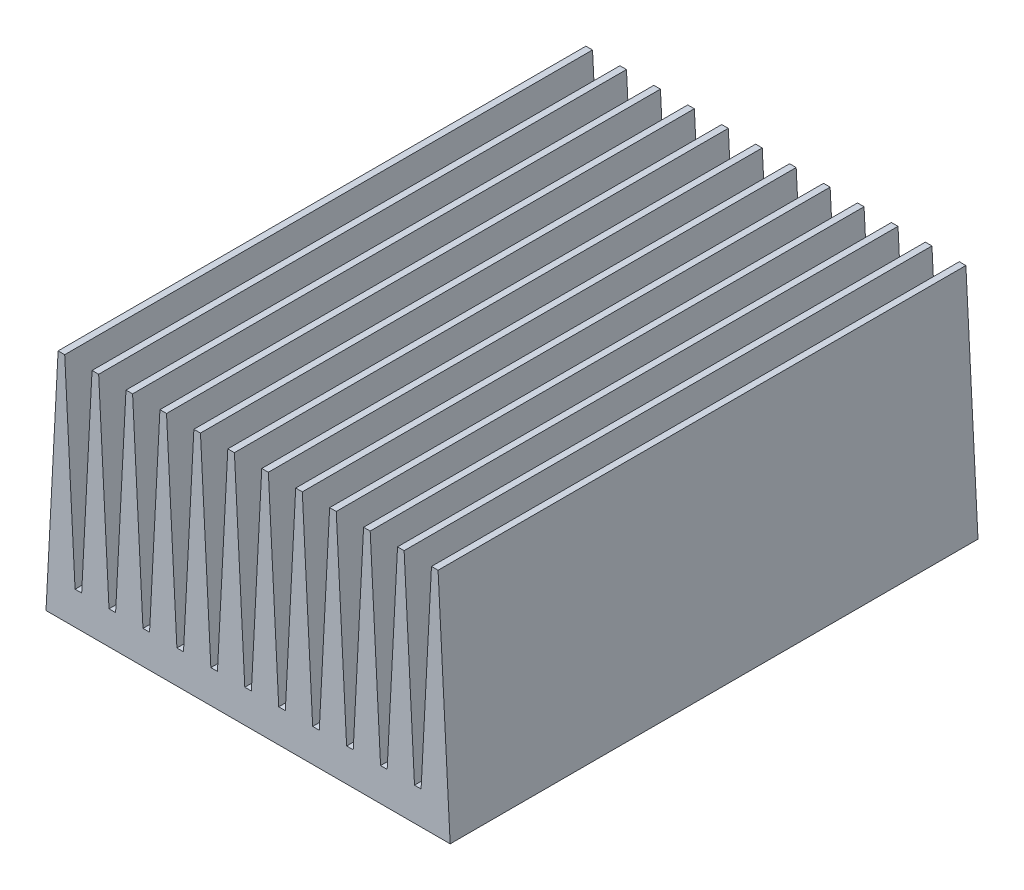
SolidWorks part; units mm, degrees
material "1060 Alloy"
ref_plane "Front Plane" through (0, 0, 0) normal (0, 0, 1) x (1, 0, 0)
ref_plane "Top Plane" through (0, 0, 0) normal (0, 1, 0) x (1, 0, 0)
ref_plane "Right Plane" through (0, 0, 0) normal (1, 0, 0) x (0, 0, -1)
sketch "Sketch1" plane through (0, 0, 0) normal (0, 0, 1) x (1, 0, 0)
  line L0 (0, 0) -> (61.2577, 0)
  line L1 (61.2577, 0) -> (59.4234, 35)
  line L2 (59.4234, 35) -> (58.4234, 35)
  line L3 (58.4234, 35) -> (56.8512, 5)
  line L4 (56.8512, 5) -> (55.8512, 5)
  line L5 (53.2789, 35) -> (51.7067, 5)
  line L6 (55.8512, 5) -> (54.2789, 35)
  line L7 (54.2789, 35) -> (53.2789, 35)
  line L8 (51.7067, 5) -> (50.7067, 5)
  line L9 (48.1345, 35) -> (46.5622, 5)
  line L10 (50.7067, 5) -> (49.1345, 35)
  line L11 (49.1345, 35) -> (48.1345, 35)
  line L12 (46.5622, 5) -> (45.5622, 5)
  line L13 (42.99, 35) -> (41.4178, 5)
  line L14 (45.5622, 5) -> (43.99, 35)
  line L15 (43.99, 35) -> (42.99, 35)
  line L16 (41.4178, 5) -> (40.4178, 5)
  line L17 (37.8455, 35) -> (36.2733, 5)
  line L18 (40.4178, 5) -> (38.8455, 35)
  line L19 (38.8455, 35) -> (37.8455, 35)
  line L20 (36.2733, 5) -> (35.2733, 5)
  line L21 (32.7011, 35) -> (31.1288, 5)
  line L22 (35.2733, 5) -> (33.7011, 35)
  line L23 (33.7011, 35) -> (32.7011, 35)
  line L24 (31.1288, 5) -> (30.1288, 5)
  line L25 (27.5566, 35) -> (25.9844, 5)
  line L26 (30.1288, 5) -> (28.5566, 35)
  line L27 (28.5566, 35) -> (27.5566, 35)
  line L28 (25.9844, 5) -> (24.9844, 5)
  line L29 (22.4121, 35) -> (20.8399, 5)
  line L30 (24.9844, 5) -> (23.4121, 35)
  line L31 (23.4121, 35) -> (22.4121, 35)
  line L32 (20.8399, 5) -> (19.8399, 5)
  line L33 (17.2677, 35) -> (15.6954, 5)
  line L34 (19.8399, 5) -> (18.2677, 35)
  line L35 (18.2677, 35) -> (17.2677, 35)
  line L36 (15.6954, 5) -> (14.6954, 5)
  line L37 (12.1232, 35) -> (10.551, 5)
  line L38 (14.6954, 5) -> (13.1232, 35)
  line L39 (13.1232, 35) -> (12.1232, 35)
  line L40 (10.551, 5) -> (9.551, 5)
  line L41 (6.9787, 35) -> (5.4065, 5)
  line L42 (9.551, 5) -> (7.9787, 35)
  line L43 (7.9787, 35) -> (6.9787, 35)
  line L44 (5.4065, 5) -> (4.4065, 5)
  line L45 (1.8343, 35) -> (0.262, 5)
  line L46 (4.4065, 5) -> (2.8343, 35)
  line L47 (2.8343, 35) -> (1.8343, 35)
  line L48 (0.262, 5) -> (0, 0)
  line L49 (0.262, 5) -> (-0.738, 5) [skipped]
  point P0 (86.0188, 0)
  point P3 (0, 0)
  dimension "D2" = 87
  dimension "D3" = 1
  dimension "D6" = 1
  dimension "D1" = 93
  dimension "D4" = 5
  dimension "D5" = 35
  dimension "D8" = 12
extrude "Boss-Extrude1" add sketch "Sketch1" along normal blind 80
equation "\"A\" = 35"
equation "\"B\" = 80"
equation "\"C\"= 1"
equation "\"D3@Sketch1\"=\"C\""
equation "\"D6@Sketch1\"=\"C\""
equation "\"D5@Sketch1\"=\"A\""
equation "\"D1@Boss-Extrude1\"=\"B\""
